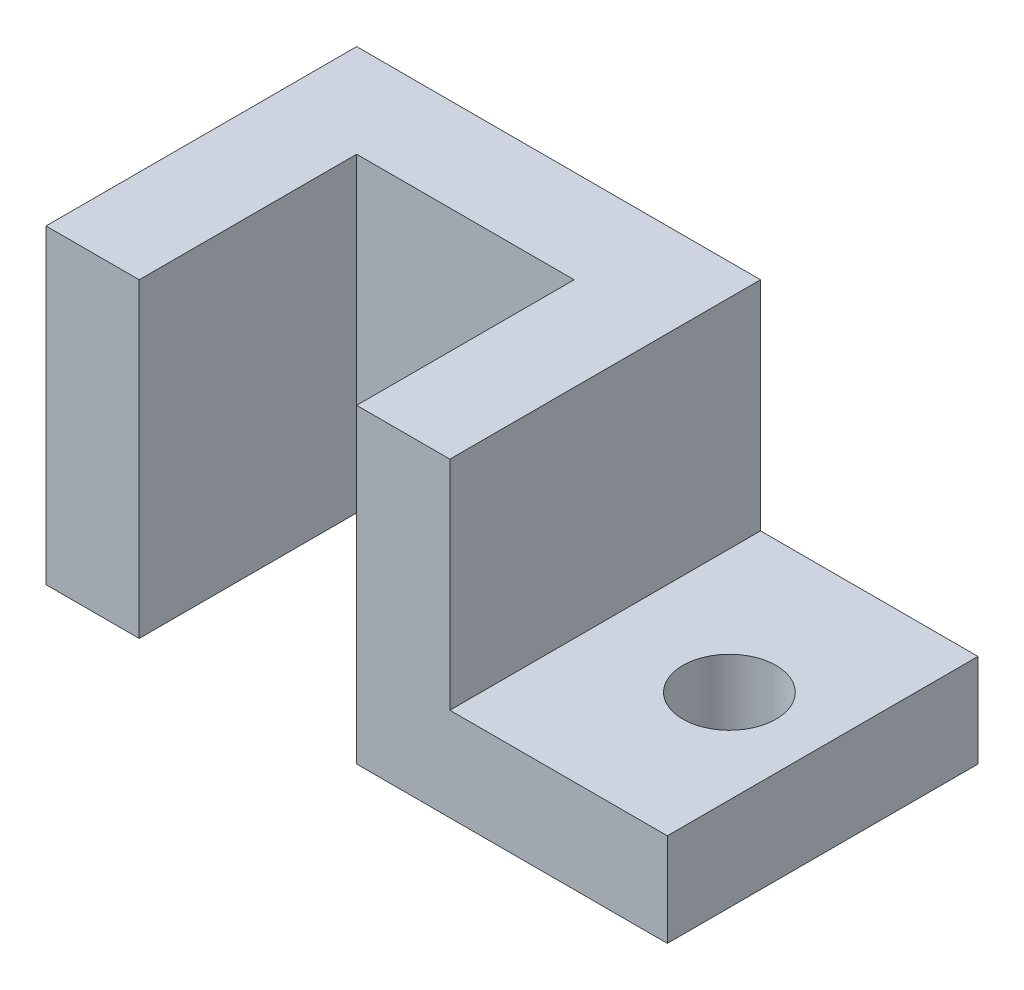
SolidWorks part; units mm, degrees
ref_plane "Front Plane" through (0, 0, 0) normal (0, 0, 1) x (1, 0, 0)
ref_plane "Top Plane" through (0, 0, 0) normal (0, 1, 0) x (1, 0, 0)
ref_plane "Right Plane" through (0, 0, 0) normal (1, 0, 0) x (0, 0, -1)
sketch "Sketch1" plane through (0, 0, 0) normal (0, 0, 1) x (1, 0, 0)
  line L0 (0, 0) -> (63.5, 0)
  line L1 (63.5, 0) -> (63.5, 19.05)
  line L2 (63.5, 19.05) -> (19.05, 19.05)
  line L3 (19.05, 19.05) -> (19.05, 63.5)
  line L4 (19.05, 63.5) -> (0, 63.5)
  line L5 (0, 63.5) -> (0, 0)
  point P2 (0, 0)
  point P7 (0, 0)
  dimension "D1" = 63.5
  dimension "D2" = 19.05
  dimension "D3" = 63.5
  dimension "D4" = 19.05
extrude "Boss-Extrude1" add sketch "Sketch1" along normal blind 63.5 contours L3 L4 L5 L0 L1 L2
sketch "Sketch2" plane through (0, 63.5, 0) normal (0, 1, 0) x (1, 0, 0)
  line L0 (0, 0) -> (-63.5, 0)
  line L1 (-63.5, 0) -> (-63.5, -63.5)
  line L2 (-63.5, -63.5) -> (-44.45, -63.5)
  line L3 (-44.45, -63.5) -> (-44.45, -19.05)
  line L4 (-44.45, -19.05) -> (0, -19.05)
  line L5 (0, -63.5) -> (0, 0) construction
  line L6 (0, -19.05) -> (0, 0)
  dimension "D1" = 63.5
  dimension "D2" = 63.5
  dimension "D3" = 19.05
  dimension "D4" = 19.05
extrude "Boss-Extrude2" add sketch "Sketch2" against normal blind 63.5
sketch "Sketch7" plane through (0, 19.05, 0) normal (0, 1, 0) x (1, 0, 0)
  line L0 (63.5, -63.5) -> (63.5, 0) construction
  line L1 (63.5, -63.5) -> (19.05, -63.5) construction
  circle A0 centre (44.4409, -31.75) radius 9.525
  dimension "D1" = 19.05
  dimension "D2" = 19.0591
  dimension "D3" = 31.75
extrude "Cut-Extrude1" cut sketch "Sketch7" against normal through all
